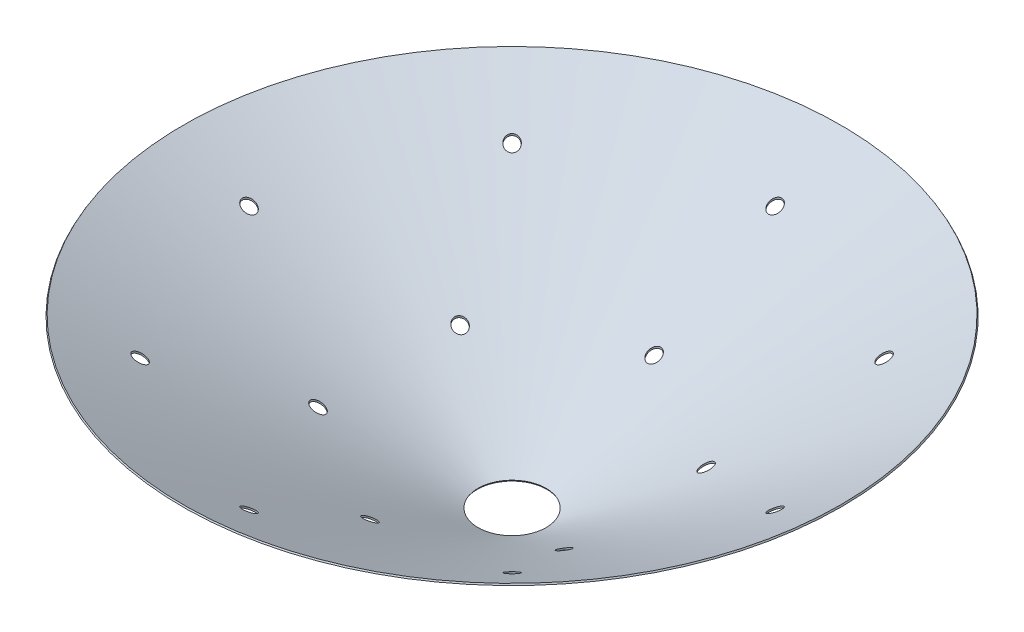
SolidWorks part; units mm, degrees
material "1.4301 (X5CrNi18-10)"
ref_plane "Ebene vorne" through (0, 0, 0) normal (0, 0, 1) x (1, 0, 0)
ref_plane "Ebene oben" through (0, 0, 0) normal (0, 1, 0) x (1, 0, 0)
ref_plane "Ebene rechts" through (0, 0, 0) normal (1, 0, 0) x (0, 0, -1)
sketch "Skizze1" plane through (0, 0, 0) normal (0, 0, 1) x (1, 0, 0)
  line L0 (-626.4798, 882.3904) -> (-625, 885)
  line L1 (-626.4798, 882.3904) -> (-66.1798, 564.6605)
  line L2 (-625, 885) -> (-64.7, 567.2702)
  line L3 (-66.1798, 564.6605) -> (-64.7, 567.2702)
  line L4 (0, 0) -> (0, 925.4486)
  line L5 (0, 495) -> (0, 1297) construction
revolve "Rotation1" add sketch "Skizze1" angle 360 about L4
sketch "Skizze2" plane through (0, 1306, 0) normal (0, 1, 0) x (1, 0, 0)
  circle A0 centre (-353.5534, -353.5534) radius 12.5 construction
  circle A1 centre (-500, 0) radius 12.5 construction
  circle A2 centre (-353.5534, 353.5534) radius 12.5 construction
  circle A3 centre (-233.8269, 135) radius 12.5 construction
  circle A4 centre (-233.8269, -135) radius 12.5 construction
  circle A5 centre (0, -270) radius 12.5 construction
  circle A6 centre (0, -500) radius 12.5 construction
  circle A7 centre (0, 270) radius 12.5 construction
  circle A8 centre (0, 500) radius 12.5 construction
  circle A9 centre (353.5534, 353.5534) radius 12.5 construction
  circle A10 centre (233.8269, 135) radius 12.5 construction
  circle A11 centre (233.8269, -135) radius 12.5 construction
  circle A12 centre (353.5534, -353.5534) radius 12.5 construction
  circle A13 centre (500, 0) radius 12.5 construction
  circle A14 centre (-353.5534, -353.5534) radius 12.5
  circle A15 centre (-500, 0) radius 12.5
  circle A16 centre (-353.5534, 353.5534) radius 12.5
  circle A17 centre (-233.8269, 135) radius 12.5
  circle A18 centre (-233.8269, -135) radius 12.5
  circle A19 centre (0, -270) radius 12.5
  circle A20 centre (0, -500) radius 12.5
  circle A21 centre (0, 270) radius 12.5
  circle A22 centre (0, 500) radius 12.5
  circle A23 centre (353.5534, 353.5534) radius 12.5
  circle A24 centre (233.8269, 135) radius 12.5
  circle A25 centre (233.8269, -135) radius 12.5
  circle A26 centre (353.5534, -353.5534) radius 12.5
  circle A27 centre (500, 0) radius 12.5
extrude "Schnitt-Linear austragen1" cut sketch "Skizze2" against normal through all
